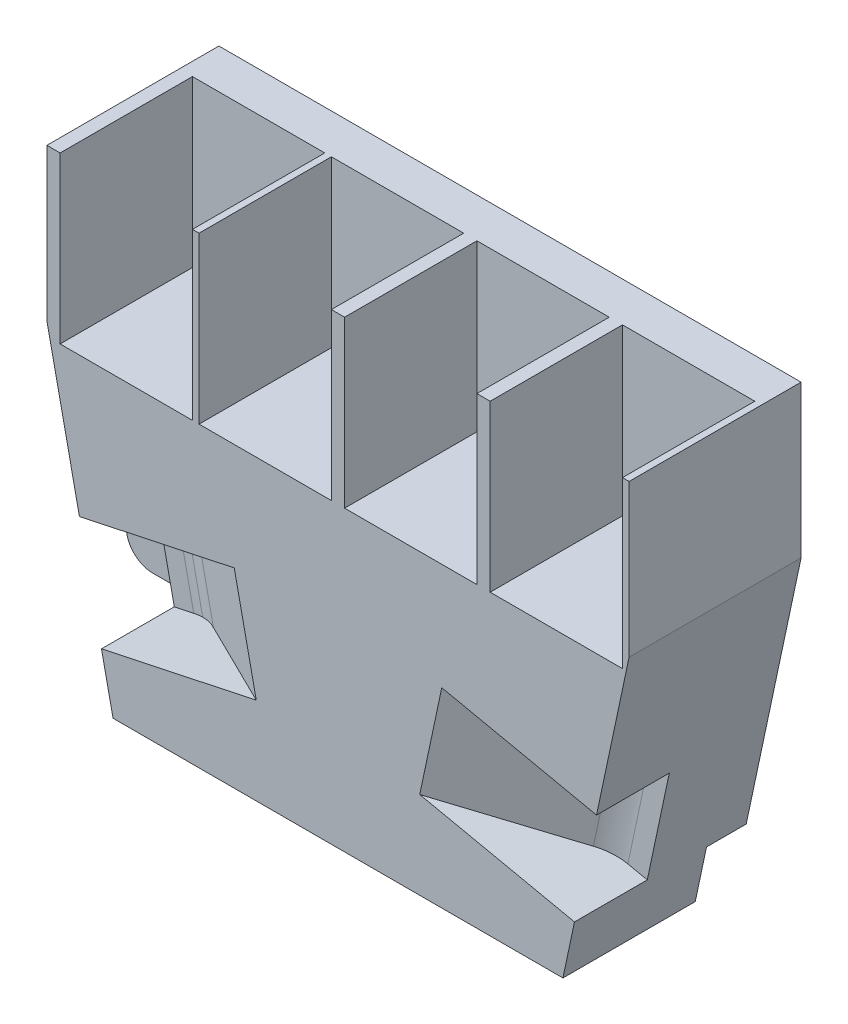
SolidWorks part; units mm, degrees
ref_plane "Front" through (0, 0, 0) normal (0, 0, 1) x (1, 0, 0)
ref_plane "Top" through (0, 0, 0) normal (0, 1, 0) x (1, 0, 0)
ref_plane "Right" through (0, 0, 0) normal (1, 0, 0) x (0, 0, -1)
sketch "草图1" plane through (0, 0, 0) normal (0, 0, 1) x (1, 0, 0)
  line L0 (-34, -24) -> (34, -24)
  line L1 (-44, 46) -> (44, 46)
  line L2 (-44, 46) -> (-44, 23)
  line L4 (44, 46) -> (44, 23)
  line L5 (-66.7553, 0) -> (86.3051, 0) construction
  line L8 (-44, 23) -> (-34, -24)
  line L9 (-44, 23) -> (56.7889, 23) construction
  line L10 (34, -24) -> (44, 23)
  dimension "D1" = 88
  dimension "D3" = 44
  dimension "D4" = 68
  dimension "D5" = 34
  dimension "D6" = 24
extrude "凸台-拉伸1" add sketch "草图1" along normal blind 26
sketch "草图2" plane through (-37.4127, -7.9602, 0) normal (-0.9781, -0.2081, 0) x (0, 0, 1)
  line L0 (13, -16.3989) -> (13, 31.6532) construction
  line L1 (26, -16.3989) -> (0, -16.3989) construction
  line L2 (26, 31.6532) -> (0, 31.6532) construction
  line L3 (0, 0) -> (26, 0)
  line L4 (26, 31.6532) -> (26, -16.3989) construction
sketch "草图3" plane through (0, 0, 0) normal (0, 0, -1) x (-1, 0, 0)
  line L0 (0, -24) -> (0, 47.0389) construction
  line L1 (34, -24) -> (-34, -24) construction
  line L3 (-20, -24) -> (20, -24)
  line L4 (-20, -24) -> (-20, 12)
  line L5 (-20, 12) -> (20, 12)
  line L6 (20, -24) -> (20, 12)
  dimension "D1" = 36
  dimension "D2" = 40
  dimension "D3" = 20
extrude "切除-拉伸4" cut sketch "草图3" against normal blind 20
sketch "草图4" plane through (0, 46, 0) normal (0, 1, 0) x (1, 0, 0)
  line L0 (44, -26) -> (-44, -26) construction
  line L1 (43, -26) -> (23, -26)
  line L2 (43, -26) -> (43, -6)
  line L3 (43, -6) -> (23, -6)
  line L4 (23, -26) -> (23, -6)
  line L5 (44, -26) -> (44, 0) construction
  line L6 (21, -26) -> (1, -26)
  line L7 (21, -26) -> (21, -6)
  line L8 (21, -6) -> (1, -6)
  line L9 (1, -26) -> (1, -6)
  line L10 (-1, -26) -> (-21, -26)
  line L11 (-1, -26) -> (-1, -6)
  line L12 (-1, -6) -> (-21, -6)
  line L13 (-21, -26) -> (-21, -6)
  line L14 (-22, -26) -> (-42, -26)
  line L15 (-22, -26) -> (-22, -6)
  line L16 (-22, -6) -> (-42, -6)
  line L17 (-42, -26) -> (-42, -6)
  dimension "D1" = 20
  dimension "D2" = 21
  dimension "D3" = 20
  dimension "D4" = 20
  dimension "D5" = 20
  dimension "D6" = 2
  dimension "D7" = 2
  dimension "D8" = 20
  dimension "D9" = 20
  dimension "D10" = 20
  dimension "D11" = 21
  dimension "D12" = 20
extrude "切除-拉伸5" cut sketch "草图4" against normal blind 25
sketch3d "3D草图5"
  line L0 (-37.3866, -7.9546, 26.004) -> (-19.9225, -4.2388, 26.004) construction
  line L1 (-37.4127, -7.9602, 0) -> (-37.4127, -7.9602, 26) construction
  line L2 (-37.3866, -7.9546, 26.004) -> (-37.4127, -7.9602, 12.8891) construction
  line L3 (-26.6334, -5.6667, 23.004) -> (-26.6334, -5.6667, 31.004)
  line L4 (-26.6334, -5.6667, 31.004) -> (-34.4583, -7.3315, 31.004)
  arc A0 (-26.6334, -5.6667, 23.004) -> (-34.4583, -7.3315, 31.004) centre (-34.4583, -7.3315, 23.004) ccw
  point P2 (-36.1231, 0.4933, 23.004)
  dimension "D1" = 3
  dimension "D2" = 3
extrude "切除-拉伸3" cut sketch "3D草图5" along direction (0.2081, -0.9781, 0) on the side against the normal mid plane 16
sketch "草图6" plane through (37.4127, -7.9602, 0) normal (0.9781, -0.2081, 0) x (0, 0, -1)
  line L0 (0, 0) -> (-26, 0)
  line L1 (-26, -16.3989) -> (-26, 31.6532) construction
sketch3d "3D草图6"
  line L0 (37.4127, -7.9602, 0) -> (37.4127, -7.9602, 26) construction
  line L2 (37.4127, -7.9602, 26) -> (26.6536, -5.671, 25.9966) construction
  line L3 (34.4784, -7.3358, 14.9991) -> (44.8243, -9.5371, 14.9991)
  line L4 (34.4784, -7.3358, 29) -> (44.8243, -9.5371, 29)
  line L5 (44.8243, -9.5371, 29) -> (44.8243, -9.5371, 14.9991)
  line L6 (26.6536, -5.671, 22.9991) -> (26.6536, -5.671, 29)
  line L7 (26.6536, -5.671, 29) -> (34.4784, -7.3358, 29)
  arc A0 (34.4784, -7.3358, 14.9991) -> (26.6536, -5.671, 22.9991) centre (34.4784, -7.3358, 22.9991) ccw
  point P2 (36.1433, 0.489, 22.9991)
  dimension "D1" = 3
  dimension "D2" = 3
extrude "切除-拉伸6" cut sketch "3D草图6" along direction (0.2081, 0.9781, 0) on the side against the normal mid plane 16
sketch "草图7" plane through (-1.6649, 7.8248, 0) normal (0.2081, -0.9781, 0) x (0.9781, 0.2081, 0)
  line L0 (-38.2502, 0) -> (-38.2502, 26) construction
  line L1 (-38.2502, 26) -> (28.261, 26) construction
  line L2 (-38.2502, 26) -> (-29.5933, 17.3431) construction
  line L3 (-24.5567, 20) -> (-31.2008, 16.1005)
  line L4 (-24.5567, 20) -> (-10.0872, 28.4922)
  line L5 (-10.0872, 28.4922) -> (-33.6713, 30.8426)
  line L6 (-35.2502, 15) -> (-43.2502, 15)
  line L7 (-43.2502, 15) -> (-43.2502, 23)
  arc A0 (-35.2502, 15) -> (-31.2008, 16.1005) centre (-35.2502, 23) ccw
  arc A1 (-33.6713, 30.8426) -> (-43.2502, 23) centre (-35.2502, 23) ccw
  dimension "D3" = 16
  dimension "D1" = 3
  dimension "D2" = 3
extrude "切除-拉伸7" cut sketch "草图7" along normal blind 16
sketch "草图11" plane through (-1.6649, -7.8248, 0) normal (0.2081, 0.9781, 0) x (0.9781, -0.2081, 0)
  line L0 (-28.261, -26) -> (38.2502, -26) construction
  line L1 (38.2502, 0) -> (38.2502, -26) construction
  line L2 (24.5567, -20) -> (31.2008, -16.1005) construction
  line L3 (31.2008, -16.1005) -> (14.3336, -26)
  line L4 (14.3336, -26) -> (32.6666, -30.5713)
  line L5 (35.2502, -15) -> (38.2502, -14.9991)
  line L6 (38.2502, -14.9991) -> (40.4608, -16.9296)
  arc A0 (32.6666, -30.5713) -> (40.4608, -16.9296) centre (35.2502, -23) ccw
  arc A1 (35.2502, -15) -> (31.2008, -16.1005) centre (35.2502, -23) ccw
  dimension "D1" = 3
  dimension "D2" = 3
extrude "切除-拉伸8" cut sketch "草图11" along normal blind 16
sketch "草图12" plane through (0, 0, 0) normal (0, 0, -1) x (-1, 0, 0)
  line L7 (-34, -24) -> (-26, -24)
  line L9 (-34, -16) -> (-30, -16)
  line L10 (-26, -24) -> (-26, -20)
  line L11 (-34, -16) -> (-39.0072, -16)
  line L13 (-34, -24) -> (-39.0072, -24)
  line L14 (-39.0072, -16) -> (-39.0072, -24)
  arc A1 (-26, -20) -> (-30, -16) centre (-30, -20) ccw
extrude "切除-拉伸10" cut sketch "草图12" against normal blind 6
sketch "草图13" plane through (0, 0, 0) normal (0, 0, -1) x (-1, 0, 0)
  line L0 (34, -24) -> (34, 21.0177) construction
  line L2 (34, -16) -> (42, -16)
  line L3 (34, -16) -> (34, -8)
  line L4 (34, -8) -> (38, -8)
  line L6 (38, -8) -> (42, -8)
  arc A0 (42, -16) -> (42, -8) centre (42, -12) ccw
  dimension "D2" = 8
extrude "凸台-拉伸3" add sketch "草图13" against normal blind 12
sketch "草图14" plane through (0, 0, 0) normal (0, 0, -1) x (-1, 0, 0)
  line L0 (37.4043, -8) -> (51.0585, -8)
  line L1 (51.0585, -8) -> (50.9518, -15.8066)
  line L2 (50.9518, -15.8066) -> (42, -16)
  line L3 (42, -16) -> (35.7021, -16)
  line L4 (35.7021, -16) -> (37.4043, -8)
extrude "切除-拉伸11" cut sketch "草图14" against normal blind 8
